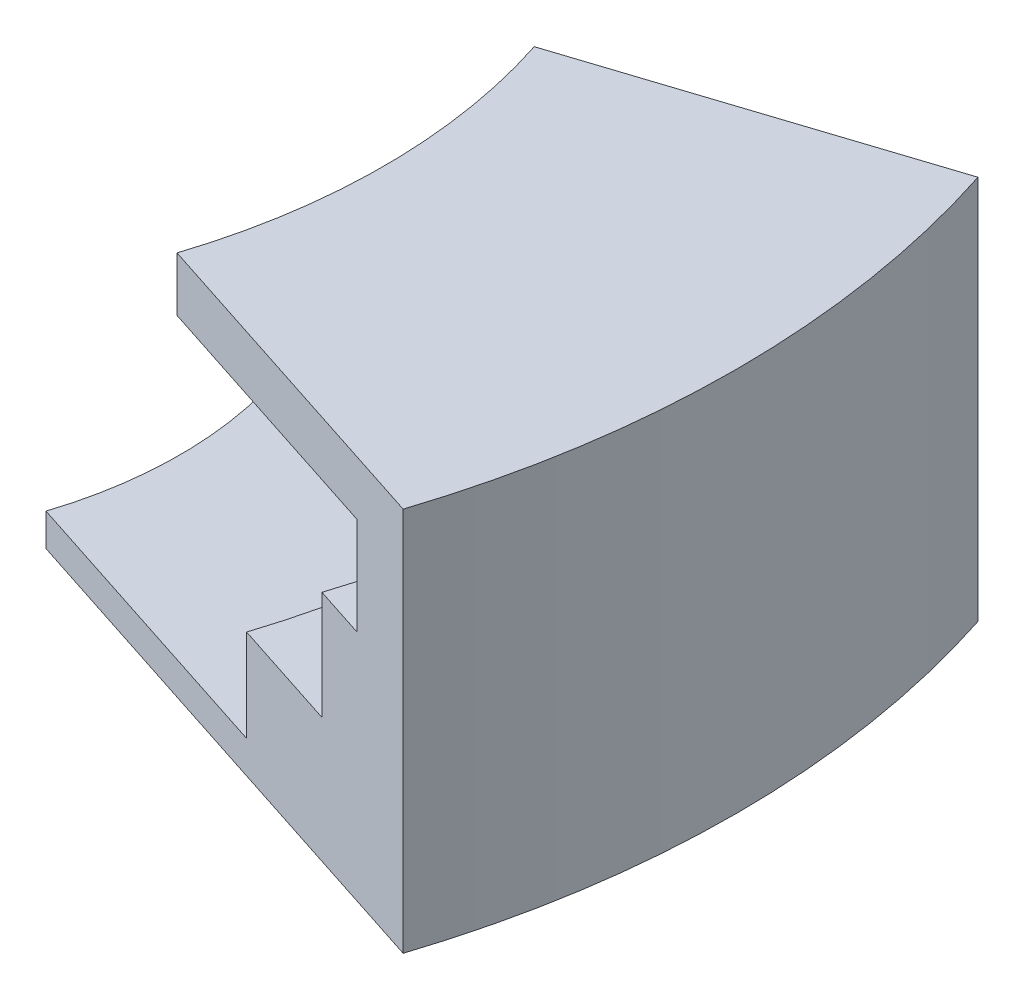
SolidWorks part; units mm, degrees
ref_plane "Front Plane" through (0, 0, 0) normal (0, 0, 1) x (1, 0, 0)
ref_plane "Top Plane" through (0, 0, 0) normal (0, 1, 0) x (1, 0, 0)
ref_plane "Right Plane" through (0, 0, 0) normal (1, 0, 0) x (0, 0, -1)
sketch "Sketch2" plane through (0, 0, 0) normal (0, 0, 1) x (1, 0, 0)
  line L0 (10.35, 112.5396) -> (19, 112.5396)
  line L1 (23.75, 118.0896) -> (23.75, 120.7896)
  line L2 (15.75, 120.7896) -> (21.75, 120.7896) construction
  line L3 (23.75, 120.7896) -> (16, 120.7896)
  line L4 (16, 120.7896) -> (16, 122.2896)
  line L5 (16, 122.2896) -> (25.75, 122.2896)
  line L6 (25.75, 122.2896) -> (25.75, 111.6396)
  line L7 (25.75, 111.6396) -> (10.35, 111.6396)
  line L8 (10.35, 111.6396) -> (10.35, 112.5396)
  line L10 (16.0956, 111.6396) -> (13.6956, 111.6396) construction
  line L11 (23.75, 118.0896) -> (22.25, 118.0896)
  line L12 (22.25, 118.0896) -> (22.25, 115.0896)
  line L13 (22.25, 115.0896) -> (19, 115.0896)
  line L14 (19, 115.0896) -> (19, 112.5396)
  line L16 (0, -1000) -> (0, 49000) construction
  line L17 (18, 121.7896) -> (18, 118.7896) construction
  line L18 (13.6956, 111.6396) -> (9.5387, 111.6396) construction
  point P1 (22.25, 115.0697)
  point P15 (11.0952, 111.6396)
  point P18 (16.4693, 120.7896)
  dimension "D1" = 1.5
  dimension "D2" = 2
  dimension "D3" = 2
  dimension "D4" = 1.5
  dimension "D5" = 3
  dimension "D6" = 0.5
  dimension "D7" = 2.7
  dimension "D8" = 1
revolve "Revolve1" add sketch "Sketch2" angle 18 about L16
